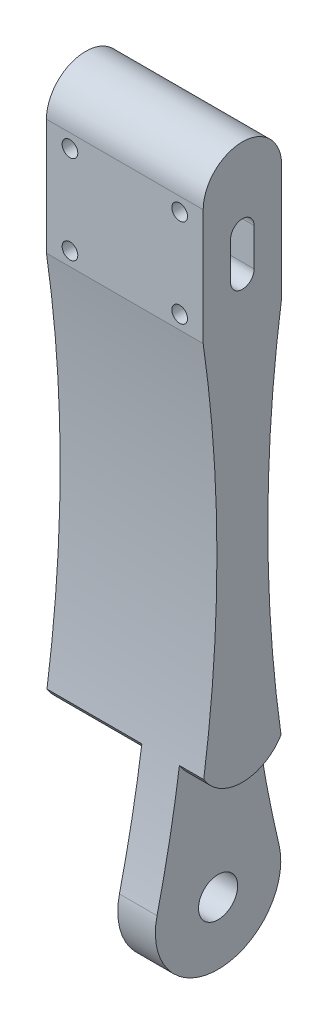
SolidWorks part; units mm, degrees
ref_plane "Front Plane" through (0, 0, 0) normal (0, 0, 1) x (1, 0, 0)
ref_plane "Top Plane" through (0, 0, 0) normal (0, 1, 0) x (1, 0, 0)
ref_plane "Right Plane" through (0, 0, 0) normal (1, 0, 0) x (0, 0, -1)
sketch "Sketch1" plane through (0, 0, 0) normal (1, 0, 0) x (0, 0, -1)
  line L3 (-5, 22.2701) -> (-5, 7.4756)
  line L4 (5, 22.2701) -> (5, 7.4756)
  line L6 (1.5, 12.4756) -> (1.5, 17.2701)
  line L7 (-1.5, 12.4756) -> (-1.5, 17.2701)
  arc A0 (1.5, 17.2701) -> (-1.5, 17.2701) centre (0, 17.2701) ccw
  arc A1 (-7.7864, -55.8936) -> (7.7864, -55.8936) centre (0, -57.7299) ccw
  arc A2 (-7.7864, -55.8936) -> (-5, 7.4756) centre (-173.2474, -16.8723) ccw
  arc A4 (5, 7.4756) -> (7.7864, -55.8936) centre (173.2474, -16.8723) ccw
  circle A5 centre (0, -57.7299) radius 2.5
  arc A6 (5, 22.2701) -> (-5, 22.2701) centre (0, 22.2701) ccw
  arc A7 (-1.5, 12.4756) -> (1.5, 12.4756) centre (0, 12.4756) ccw
extrude "Boss-Extrude1" add sketch "Sketch1" along normal blind 20
sketch "Sketch24" plane through (0, 0, 0) normal (0, 0, 1) x (1, 0, 0)
  line L1 (0, -65.7299) -> (8.1, -65.7299)
  line L2 (0, -65.7299) -> (0, -40.7299)
  line L3 (0, -40.7299) -> (8.1, -40.7299)
  line L4 (8.1, -65.7299) -> (8.1, -40.7299)
  line L5 (20, -65.7299) -> (16.9, -65.7299)
  line L6 (20, -65.7299) -> (20, -40.7299)
  line L7 (20, -40.7299) -> (16.9, -40.7299)
  line L8 (16.9, -65.7299) -> (16.9, -40.7299)
extrude "Cut-Extrude14" cut sketch "Sketch24" against normal through all and the other way through all
sketch "Sketch25" plane through (0, 0, -5) normal (0, 0, -1) x (-1, 0, 0)
  circle A0 centre (-17, 9.2256) radius 1
  circle A1 centre (-17, 20.5201) radius 1
  circle A2 centre (-3, 9.2256) radius 1
  circle A3 centre (-3, 20.5201) radius 1
extrude "Cut-Extrude15" cut sketch "Sketch25" along normal through all and the other way through all
sketch "Sketch31" plane through (0, 0, 5) normal (0, 0, 1) x (1, 0, 0)
  line L0 (8.1, -65.7299) -> (16.9, -65.7299) construction
  line L1 (8.1, -40.7299) -> (12.1, -40.7299)
  line L2 (8.1, -40.7299) -> (8.1, -65.7299)
  line L3 (8.1, -65.7299) -> (12.1, -65.7299)
  line L4 (12.1, -40.7299) -> (12.1, -65.7299)
extrude "Cut-Extrude17" cut sketch "Sketch31" against normal through all and the other way through all
sketch "Sketch26" plane through (20, 0, 0) normal (1, 0, 0) x (0, 0, -1)
  line L1 (-4.9298, -40.7299) -> (4.9298, -40.7299)
  arc A1 (-4.9298, -40.7299) -> (4.9298, -40.7299) centre (0, -37.7299) ccw
extrude "Boss-Extrude5" add sketch "Sketch26" against normal through all
sketch "Sketch32" plane through (12.1, 0, 0) normal (-1, 0, 0) x (0, 0, 1)
  line L2 (-2.5, -53.2274) -> (-2.5, -42.9311)
  line L3 (-2.5, -42.9311) -> (2.5, -42.9311)
  line L4 (2.5, -53.2274) -> (2.5, -42.9311)
  circle A0 centre (0, -57.7299) radius 2.5
  arc A1 (-2.5, -53.2274) -> (2.5, -53.2274) centre (0, -57.7299) ccw
  arc A2 (-4.9298, -40.7299) -> (4.9298, -40.7299) centre (0, -37.7299) ccw construction
extrude "Boss-Extrude6" add sketch "Sketch32" along normal blind 2
